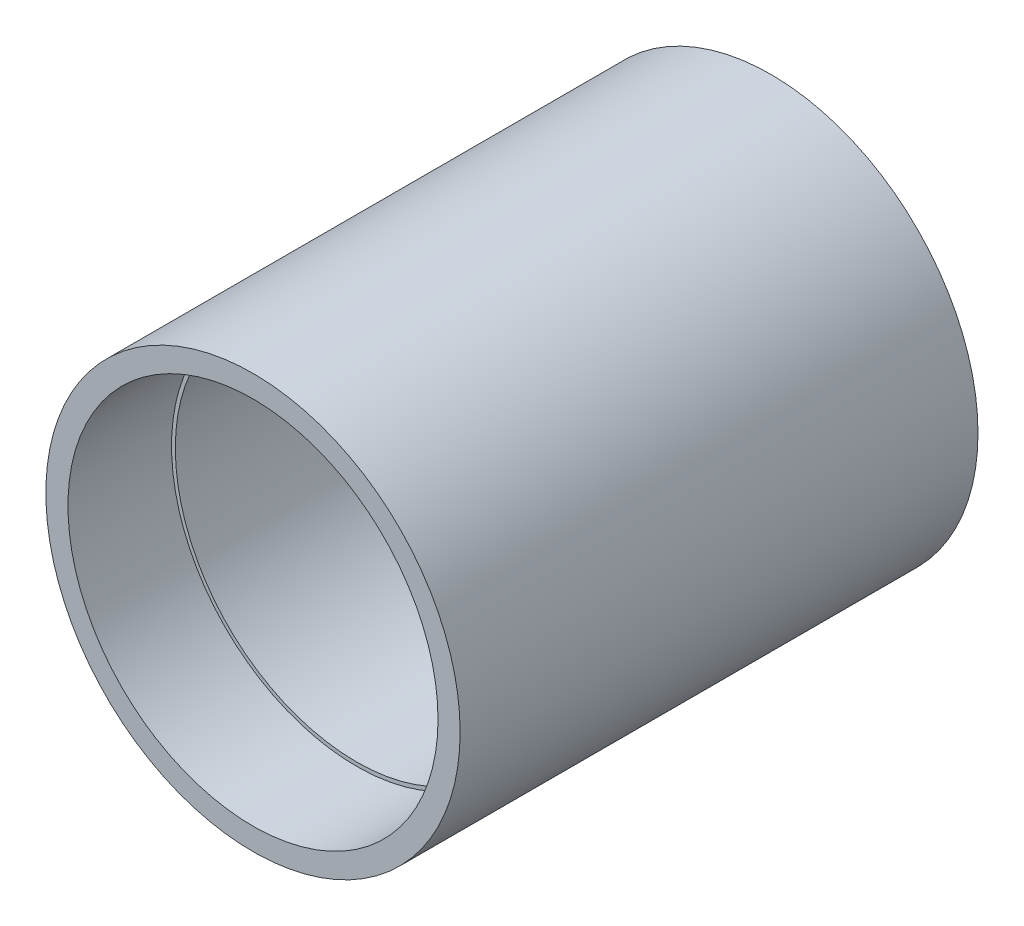
SolidWorks part; units mm, degrees
ref_plane "Ebene vorne" through (0, 0, 0) normal (0, 0, 1) x (1, 0, 0)
ref_plane "Ebene oben" through (0, 0, 0) normal (0, 1, 0) x (1, 0, 0)
ref_plane "Ebene rechts" through (0, 0, 0) normal (1, 0, 0) x (0, 0, -1)
sketch "Skizze1" plane through (0, 0, 0) normal (0, 0, 1) x (1, 0, 0)
  circle A0 centre (0, 0) radius 40
  circle A1 centre (0, 0) radius 35
  dimension "D1" = 80
  dimension "D2" = 70
extrude "Aufsatz-Linear austragen1" add sketch "Skizze1" along normal blind 100
sketch "Skizze4" plane through (0, 0, 100) normal (0, 0, 1) x (1, 0, 0)
  circle A0 centre (0, 0) radius 35.73
  point P3 (-35.73, 0)
  point P4 (0, 35.73)
  point P5 (35.73, 0)
  point P6 (0, -35.73)
  dimension "D1" = 71.46
extrude "Schnitt-Linear austragen1" cut sketch "Skizze4" against normal blind 20
cosmetic thread "Gewindedarstellung1" parameters "D2"=72
thread "Gewinde1" pitch 0.5 start angle 0, offset 1, length 0, pitch 0.5, diameter 71.46
ref_plane "Ebene3" through (-35.73, 0, 101) normal (0, -1, 0) x (-1, 0, 0)
sketch "Gewindeprofil3" [suppressed] plane through (-35.73, 0, 101) normal (0, -1, 0) x (-1, 0, 0)
  line L0 (0, 0) -> (0, 0.5) construction
  line L1 (0, 0) -> (0.2706, 0.1562)
  line L2 (0.2706, 0.1562) -> (0.2706, 0.2187)
  line L3 (0.2706, 0.2187) -> (0, 0.375)
  line L4 (0.2706, 0.1875) -> (0, 0.1875) construction
  line L11 (0, 0) -> (0, 0.375)
  point P2 (0, 0)
  dimension "Pitch" = 0.5
  dimension "Profile_Angle" = 60
  dimension "Profile_Land" = 0.0625
  dimension "Profile_Height" = 0.2706
